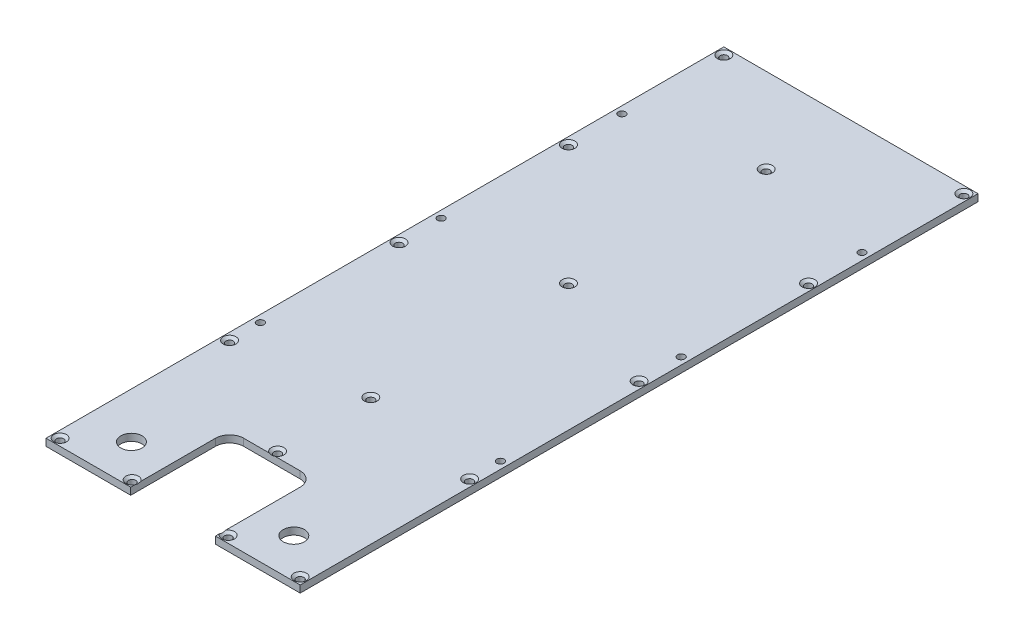
SolidWorks part; units mm, degrees
material "6061 Alloy"
ref_plane "Front Plane" through (0, 0, 0) normal (0, 0, 1) x (1, 0, 0)
ref_plane "Top Plane" through (0, 0, 0) normal (0, 1, 0) x (1, 0, 0)
ref_plane "Right Plane" through (0, 0, 0) normal (1, 0, 0) x (0, 0, -1)
sketch "Sketch1" plane through (0, 0, 0) normal (0, 1, 0) x (1, 0, 0)
  line L0 (-57.15, -171.45) -> (-57.15, 152.4)
  line L1 (-57.15, 152.4) -> (57.15, 152.4)
  line L2 (57.15, 152.4) -> (57.15, -171.45)
  line L3 (57.15, -171.45) -> (19.05, -171.45)
  line L4 (19.05, -171.45) -> (19.05, -107.95)
  line L5 (19.05, -107.95) -> (-19.05, -107.95)
  line L6 (-19.05, -107.95) -> (-19.05, -171.45)
  line L7 (-19.05, -171.45) -> (-57.15, -171.45)
  dimension "D1" = 114.3
  dimension "D2" = 323.85
  dimension "D3" = 38.1
  dimension "D4" = 38.1
  dimension "D5" = 63.5
  dimension "D6" = 57.15
  dimension "D7" = 152.4
extrude "Extrude1" add sketch "Sketch1" along normal blind 3.175
hole_wizard "CSK for #4 Flat Head Machine Screw (100)1" positions "3DSketch1" profile "Sketch3" countersink size "#4" standard "Ansi Inch" end condition through all
sketch3d "3DSketch1"
  line L0 (-57.15, 3.175, -152.4) -> (-57.15, 3.175, 171.45) construction
  line L1 (57.15, 3.175, -152.4) -> (-57.15, 3.175, -152.4) construction
  line L2 (57.15, 3.175, 171.45) -> (57.15, 3.175, -152.4) construction
  line L8 (-19.05, 3.175, 171.45) -> (-19.05, 3.175, 107.95) construction
  line L9 (-19.05, 3.175, 107.95) -> (19.05, 3.175, 107.95) construction
  line L10 (19.05, 3.175, 107.95) -> (19.05, 3.175, 171.45) construction
  point P0 (-53.975, 3.175, -149.225)
  point P2 (53.975, 3.175, -149.225)
  point P4 (53.975, 3.175, 149.225)
  point P6 (21.59, 3.175, 149.225)
  point P8 (0, 3.175, 105.41)
  point P12 (-21.59, 3.175, 149.225)
  point P14 (-53.975, 3.175, 149.225)
  point P16 (-53.975, 3.175, -79.375)
  point P18 (-53.975, 3.175, -3.175)
  point P20 (-53.975, 3.175, 73.025)
  point P22 (53.975, 3.175, 73.025)
  point P24 (53.975, 3.175, -3.175)
  point P26 (53.975, 3.175, -79.375)
  point P28 (0, 3.175, -114.3)
  point P30 (0, 3.175, 63.5)
  point P91 (0, 3.175, -25.4)
  dimension "D1" = 3.175
  dimension "D2" = 3.175
  dimension "D3" = 3.175
  dimension "D4" = 69.85
  dimension "D9" = 2.54
  dimension "D5" = 76.2
  dimension "D6" = 76.2
  dimension "D7" = 76.2
  dimension "D8" = 2.54
  dimension "D13" = 88.9
  dimension "D10" = 2.54
  dimension "D11" = 38.1
  dimension "D12" = 88.9
sketch "Sketch3" plane through (-53.975, 3.175, -149.225) normal (1, 0, 0) x (0, 0, 1)
  line L0 (0, 0) -> (0, 3.175)
  line L1 (0, 3.175) -> (1.6319, 3.175)
  line L2 (1.6319, 3.175) -> (1.6319, 1.0284)
  line L3 (1.6319, 1.0284) -> (2.8575, 0)
  line L5 (2.8575, 0) -> (0, 0)
  line L6 (-1.6319, 1.0284) -> (-2.8575, 0) construction
  line L11 (0, -6.35) -> (0, 107.95) construction
  dimension "Thru Hole Dia." = 3.2639
  dimension "Thru Hole Depth" = 3.175
  dimension "Near C'Sink Dia." = 5.715
  dimension "Near C'Sink Angle" = 100
fillet "Fillet1" radius 6.35 1 edges at (-19.05, 1.5875, 107.95)
fillet "Fillet2" radius 6.35 1 edges at (19.05, 1.5875, 107.95)
sketch "Sketch4" plane through (0, 3.175, 0) normal (0, 1, 0) x (-1, 0, 0)
  line L1 (57.15, 171.45) -> (19.05, 171.45) construction
  line L4 (57.15, -152.4) -> (57.15, 171.45) construction
  line L5 (-57.15, 171.45) -> (-57.15, -152.4) construction
  circle A0 centre (36.5125, 134.62) radius 4.7625
  circle A1 centre (-36.5125, 134.62) radius 4.7625
  dimension "D1" = 20.6375
  dimension "D2" = 36.83
  dimension "D3" = 20.6375
extrude "Cut-Extrude1" cut sketch "Sketch4" against normal through all
sketch "Sketch5" plane through (0, 3.175, 0) normal (0, 1, 0) x (-1, 0, 0)
  line L0 (-57.15, 171.45) -> (-57.15, -152.4) construction
  line L1 (57.15, 171.45) -> (-57.15, 171.45)
  line L2 (57.15, 171.45) -> (57.15, 152.4)
  line L3 (57.15, 152.4) -> (-57.15, 152.4)
  line L4 (-57.15, 171.45) -> (-57.15, 152.4)
  dimension "D1" = 19.05
extrude "Cut-Extrude2" cut sketch "Sketch5" against normal through all
hole_wizard "#4 Clearance Hole1" positions "3DSketch2" profile "Sketch6" hole size "#4" standard "Ansi Inch"
sketch3d "3DSketch2"
  line L0 (57.15, 3.175, -152.4) -> (-57.15, 3.175, -152.4) construction
  line L1 (-57.15, 3.175, -152.4) -> (-57.15, 3.175, 152.4) construction
  line L2 (57.15, 3.175, 152.4) -> (57.15, 3.175, -152.4) construction
  point P0 (-53.975, 3.175, -103.378)
  point P2 (53.975, 3.175, -103.378)
  point P4 (53.975, 3.175, -22.098)
  point P6 (-53.975, 3.175, -22.098)
  point P8 (-53.975, 3.175, 59.182)
  point P10 (53.975, 3.175, 59.182)
  dimension "D1" = 49.022
  dimension "D2" = 3.175
  dimension "D3" = 3.175
  dimension "D4" = 81.28
  dimension "D5" = 81.28
sketch "Sketch6" plane through (-53.975, 3.175, -103.378) normal (1, 0, 0) x (0, 0, 1)
  line L0 (0, 0) -> (0, 7.3306)
  line L1 (0, 7.3306) -> (1.6319, 6.35)
  line L2 (1.6319, 6.35) -> (1.6319, 0)
  line L5 (1.6319, 0) -> (0, 0)
  line L10 (0, 7.3306) -> (-1.6319, 6.35) construction
  line L11 (0, -6.35) -> (0, 107.95) construction
  dimension "Hole Dia." = 3.2639
  dimension "Hole Depth" = 6.35
  dimension "Drill Angle" = 118
